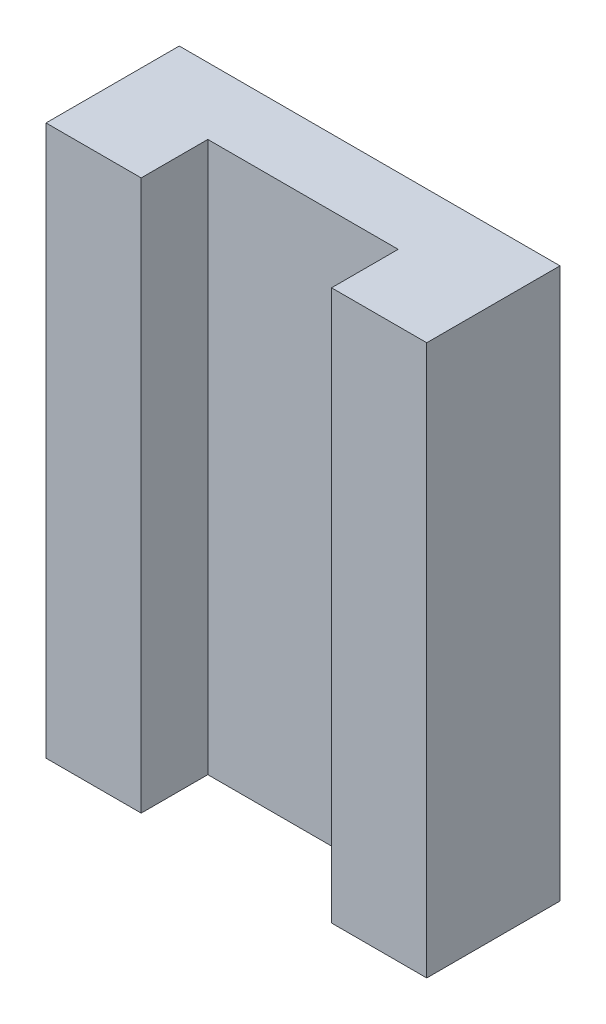
SolidWorks part; units mm, degrees
ref_plane "前视基准面" through (0, 0, 0) normal (0, 0, 1) x (1, 0, 0)
ref_plane "上视基准面" through (0, 0, 0) normal (0, 1, 0) x (1, 0, 0)
ref_plane "右视基准面" through (0, 0, 0) normal (1, 0, 0) x (0, 0, -1)
sketch "草图1" plane through (0, 0, 0) normal (0, 0, 1) x (1, 0, 0)
  line L0 (-40.6865, 36.0035) -> (-20.6865, 36.0035)
  line L1 (-20.6865, 36.0035) -> (-20.6865, 7.1035)
  line L2 (-20.6865, 7.1035) -> (-40.6865, 7.1035)
  line L3 (-40.6865, 7.1035) -> (-40.6865, 36.0035)
  dimension "D1" = 20
  dimension "D2" = 28.9
extrude "凸台-拉伸1" add sketch "草图1" along normal blind 7
sketch "草图2" plane through (0, 36.0035, 0) normal (0, 1, 0) x (1, 0, 0)
  line L0 (-30.6865, -7) -> (-35.6865, -7) construction
  line L1 (-20.6865, -7) -> (-40.6865, -7) construction
  line L2 (-30.6865, -7) -> (-35.6865, -7)
  line L3 (-35.6865, -7) -> (-35.6865, -3.5)
  line L4 (-35.6865, -3.5) -> (-25.6865, -3.5)
  line L5 (-25.6865, -3.5) -> (-25.6865, -7)
  line L6 (-25.6865, -7) -> (-30.6865, -7)
  dimension "D1" = 5
  dimension "D2" = 3.5
  dimension "D3" = 10
extrude "切除-拉伸1" cut sketch "草图2" against normal blind 30.5
sketch "草图3" plane through (0, 0, 0) normal (0, 0, -1) x (-1, 0, 0)
  line L0 (30.6865, 7.1035) -> (30.6865, 36.0035) construction
  line L1 (40.6865, 7.1035) -> (20.6865, 7.1035) construction
  line L2 (20.6865, 36.0035) -> (40.6865, 36.0035) construction
  line L3 (30.6865, 36.0035) -> (30.6865, 31.0035) construction
  line L4 (30.6865, 31.0035) -> (23.1865, 31.0035) construction
  line L5 (23.1865, 31.0035) -> (23.1865, 21.5535) construction
  line L6 (23.1865, 21.5535) -> (40.6865, 21.5535) construction
  line L7 (40.6865, 36.0035) -> (40.6865, 7.1035) construction
  circle A0 centre (23.1865, 31.0035) radius 1.5
  circle A1 centre (38.1865, 31.0035) radius 1.5
  circle A2 centre (38.1865, 12.1035) radius 1.5
  circle A3 centre (23.1865, 12.1035) radius 1.5
  dimension "D3" = 3
  dimension "D1" = 5
  dimension "D2" = 7.5
extrude "切除-拉伸2" cut sketch "草图3" against normal blind 2.5
